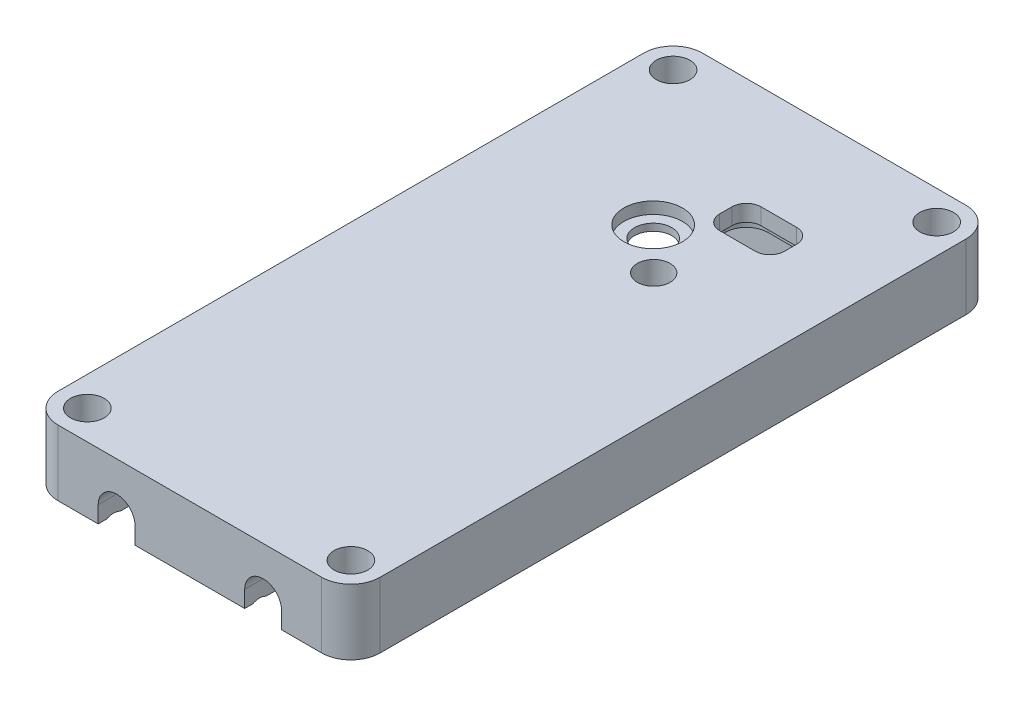
SolidWorks part; units mm, degrees
material "6061-T6 (SS)"
ref_plane "Front Plane" through (0, 0, 0) normal (0, 0, 1) x (1, 0, 0)
ref_plane "Top Plane" through (0, 0, 0) normal (0, 1, 0) x (1, 0, 0)
ref_plane "Right Plane" through (0, 0, 0) normal (1, 0, 0) x (0, 0, -1)
sketch "Sketch1" plane through (0, 0, 0) normal (0, 1, 0) x (1, 0, 0)
  line L1 (-14.127, 26.127) -> (14.127, 26.127) construction
  line L2 (-14.127, 26.127) -> (-14.127, -26.127) construction
  line L3 (-14.127, -26.127) -> (14.127, -26.127) construction
  line L4 (14.127, 26.127) -> (14.127, -26.127) construction
  line L5 (-14.127, 26.127) -> (14.127, -26.127) construction
  line L6 (-14.127, -26.127) -> (14.127, 26.127) construction
  line L7 (-17.4625, 34.925) -> (17.4625, 34.925)
  line L8 (-17.4625, 34.925) -> (-17.4625, -34.925)
  line L9 (-17.4625, -34.925) -> (17.4625, -34.925)
  line L10 (17.4625, 34.925) -> (17.4625, -34.925)
  line L11 (-17.4625, 34.925) -> (17.4625, -34.925) construction
  line L12 (-17.4625, -34.925) -> (17.4625, 34.925) construction
  point P0 (0, 0)
  point P6 (0, 0)
  dimension "D1" = 28.254
  dimension "D2" = 52.254
  dimension "D3" = 69.85
  dimension "D4" = 34.925
extrude "Boss-Extrude1" add sketch "Sketch1" along normal blind 7.112
fillet "Fillet1" radius 3.175 4 edges at (-17.4625, 3.556, -34.925) (17.4625, 3.556, -34.925) (17.4625, 3.556, 34.925) (-17.4625, 3.556, 34.925)
sketch "Sketch8" plane through (0, 0, 0) normal (0, 1, 0) x (1, 0, 0)
  line L0 (14.2875, 34.925) -> (-14.2875, 34.925) construction
  line L1 (-17.4625, 31.75) -> (-17.4625, -31.75) construction
  circle A0 centre (-1.2573, 21.6662) radius 2.3813
  dimension "D3" = 4.7625
  dimension "D1" = 13.2588
  dimension "D2" = 16.2052
extrude "Boss-Extrude2" add sketch "Sketch8" along normal up to surface (7.112 mm away) contours A0 up to face at (0, 7.112, 0)
sketch "Sketch9" plane through (0, 7.112, 0) normal (0, 1, 0) x (1, 0, 0)
  line L2 (-17.4625, 31.75) -> (-17.4625, -31.75) construction
  line L3 (14.2875, 34.925) -> (-14.2875, 34.925) construction
  circle A0 centre (-0.8255, 16.129) radius 2.0193
  dimension "D1" = 4.0386
  dimension "D2" = 18.796
  dimension "D3" = 16.637
extrude "Cut-Extrude6" cut sketch "Sketch9" against normal through all
sketch "Sketch12" plane through (0, 0, 0) normal (0, -1, 0) x (1, 0, 0)
  line L1 (14.127, 26.127) -> (-14.127, 26.127)
  line L2 (14.127, 26.127) -> (14.127, -26.127)
  line L3 (14.127, -26.127) -> (-14.127, -26.127)
  line L4 (-17.4625, 31.75) -> (-17.4625, -31.75)
  line L5 (-14.2875, -34.925) -> (14.2875, -34.925)
  line L6 (17.4625, -31.75) -> (17.4625, 31.75)
  line L7 (14.2875, 34.925) -> (-14.2875, 34.925)
  line L8 (-17.4625, 31.75) -> (-17.4625, -31.75)
  line L9 (-14.2875, -34.925) -> (14.2875, -34.925)
  line L10 (17.4625, -31.75) -> (17.4625, 31.75)
  line L11 (14.2875, 34.925) -> (-14.2875, 34.925)
  line L12 (-14.127, 26.127) -> (-14.127, -26.127)
  line L13 (14.127, 26.127) -> (-14.127, -26.127) construction
  line L14 (14.127, -26.127) -> (-14.127, 26.127) construction
  arc A4 (-17.4625, -31.75) -> (-14.2875, -34.925) centre (-14.2875, -31.75) ccw
  arc A5 (14.2875, -34.925) -> (17.4625, -31.75) centre (14.2875, -31.75) ccw
  arc A6 (17.4625, 31.75) -> (14.2875, 34.925) centre (14.2875, 31.75) ccw
  arc A7 (-14.2875, 34.925) -> (-17.4625, 31.75) centre (-14.2875, 31.75) ccw
  arc A8 (-17.4625, -31.75) -> (-14.2875, -34.925) centre (-14.2875, -31.75) ccw
  arc A9 (14.2875, -34.925) -> (17.4625, -31.75) centre (14.2875, -31.75) ccw
  arc A10 (17.4625, 31.75) -> (14.2875, 34.925) centre (14.2875, 31.75) ccw
  arc A11 (-14.2875, 34.925) -> (-17.4625, 31.75) centre (-14.2875, 31.75) ccw
  point P2 (0, 0)
  dimension "D2" = 52.254
  dimension "D3" = 28.254
  dimension "D1" = 0
extrude "Cut-Extrude8" cut sketch "Sketch12" against normal blind 4.318
fillet "Fillet2" radius 1.5875 4 edges at (-14.127, 2.159, 26.127) (-14.127, 2.159, -26.127) (14.127, 2.159, -26.127) (14.127, 2.159, 26.127)
sketch "Sketch16" plane through (0, 4.318, 0) normal (0, -1, 0) x (1, 0, 0)
  line L1 (7.789, 18.948) -> (-9.483, 18.948)
  line L2 (7.789, 18.948) -> (7.789, 2.946)
  line L3 (7.789, 2.946) -> (-9.483, 2.946)
  line L4 (-9.483, 18.948) -> (-9.483, 2.946)
  line L5 (7.789, 18.948) -> (-9.483, 2.946) construction
  line L6 (7.789, 2.946) -> (-9.483, 18.948) construction
  point P0 (-0.847, 10.947)
  dimension "D3" = 18.948
  dimension "D1" = 16.002
  dimension "D2" = 17.272
  dimension "D4" = 9.483
extrude "Boss-Extrude3" add sketch "Sketch16" along normal offset from surface (2.0574 mm away) 2.2606 up to face at (0, 0, 0)
sketch "Sketch25" plane through (0, 7.112, 0) normal (0, 1, 0) x (1, 0, 0)
  line L0 (-9.483, -15.3666) -> (7.789, -15.3666)
  line L1 (-9.483, -18.948) -> (7.789, -18.948)
  line L2 (-9.483, -18.948) -> (-9.483, -17.2716)
  line L3 (-9.483, -17.2716) -> (7.789, -17.2716)
  line L4 (7.789, -2.946) -> (-9.483, -2.946)
  line L5 (7.789, -18.948) -> (7.789, -2.946)
  line L6 (-9.483, -18.948) -> (7.789, -18.948)
  line L7 (-9.483, -2.946) -> (-9.483, -18.948)
  line L8 (7.789, -2.946) -> (-9.483, -2.946)
  line L9 (7.789, -18.948) -> (7.789, -2.946)
  line L10 (-9.483, -18.948) -> (7.789, -18.948)
  line L11 (-9.483, -2.946) -> (-9.483, -18.948)
  line L12 (7.789, -18.948) -> (7.789, -17.2716)
  line L13 (-9.483, -15.3666) -> (-9.483, -13.6902)
  line L14 (-9.483, -13.6902) -> (7.789, -13.6902)
  line L15 (7.789, -15.3666) -> (7.789, -13.6902)
  line L16 (-9.483, -11.7852) -> (7.789, -11.7852)
  line L17 (-9.483, -11.7852) -> (-9.483, -10.1088)
  line L18 (-9.483, -10.1088) -> (7.789, -10.1088)
  line L19 (7.789, -11.7852) -> (7.789, -10.1088)
  line L20 (-9.483, -8.2038) -> (7.789, -8.2038)
  line L21 (-9.483, -8.2038) -> (-9.483, -6.5274)
  line L22 (-9.483, -6.5274) -> (7.789, -6.5274)
  line L23 (7.789, -8.2038) -> (7.789, -6.5274)
  line L24 (-9.483, -4.6224) -> (7.789, -4.6224)
  line L25 (-9.483, -4.6224) -> (-9.483, -2.946)
  line L26 (-9.483, -2.946) -> (7.789, -2.946)
  line L27 (7.789, -4.6224) -> (7.789, -2.946)
  dimension "D2" = 1.905
  dimension "D1" = 0
  dimension "D3" = 5
extrude "Boss-Extrude4" [suppressed] add sketch "Sketch25" along normal offset from surface (4.0005 mm away) 11.1125 contours L1 L9 L3 L2 | L14 L11 L0 L9 | L18 L11 L16 L9 | L22 L11 L20 L9 | L11 L24 L9 L8
chamfer "Chamfer1" [suppressed] distance 4.7625 angle 45
sketch "Sketch31" plane through (0, 0, 0) normal (0, -1, 0) x (1, 0, 0)
  line L4 (-12.7, 28.575) -> (-13.0969, 28.575)
  line L5 (13.0969, 28.575) -> (12.7, 28.575)
  line L6 (16.2719, 25.4) -> (16.2719, -25.4)
  line L7 (13.0969, -28.575) -> (12.7, -28.575)
  line L8 (-16.2719, 25.4) -> (-16.2719, -25.4)
  line L9 (16.2719, 28.575) -> (-16.2719, -28.575) construction
  line L10 (16.2719, -28.575) -> (-16.2719, 28.575) construction
  line L11 (-9.525, 33.3375) -> (9.525, 33.3375)
  line L16 (-11.1125, 31.75) -> (-11.1125, 30.1625)
  line L18 (11.1125, 31.75) -> (11.1125, 30.1625)
  line L19 (-11.1125, 33.3375) -> (11.1125, 28.575) construction
  line L20 (-11.1125, 28.575) -> (11.1125, 33.3375) construction
  line L21 (-9.525, -33.3375) -> (9.525, -33.3375)
  line L22 (-11.1125, -31.75) -> (-11.1125, -30.1625)
  line L24 (11.1125, -31.75) -> (11.1125, -30.1625)
  line L25 (-11.1125, -33.3375) -> (11.1125, -28.575) construction
  line L26 (-11.1125, -28.575) -> (11.1125, -33.3375) construction
  line L27 (-12.7, -28.575) -> (-13.0969, -28.575)
  arc A4 (16.2719, -25.4) -> (13.0969, -28.575) centre (13.0969, -25.4) cw
  arc A5 (-13.0969, -28.575) -> (-16.2719, -25.4) centre (-13.0969, -25.4) cw
  arc A6 (-16.2719, 25.4) -> (-13.0969, 28.575) centre (-13.0969, 25.4) cw
  arc A7 (16.2719, 25.4) -> (13.0969, 28.575) centre (13.0969, 25.4) ccw
  arc A8 (12.7, -28.575) -> (11.1125, -30.1625) centre (12.7, -30.1625) ccw
  arc A9 (11.1125, -31.75) -> (9.525, -33.3375) centre (9.525, -31.75) cw
  arc A10 (-11.1125, -31.75) -> (-9.525, -33.3375) centre (-9.525, -31.75) ccw
  arc A11 (-12.7, -28.575) -> (-11.1125, -30.1625) centre (-12.7, -30.1625) cw
  arc A16 (-11.1125, 31.75) -> (-9.525, 33.3375) centre (-9.525, 31.75) cw
  arc A17 (-11.1125, 30.1625) -> (-12.7, 28.575) centre (-12.7, 30.1625) cw
  arc A18 (12.7, 28.575) -> (11.1125, 30.1625) centre (12.7, 30.1625) cw
  arc A19 (11.1125, 31.75) -> (9.525, 33.3375) centre (9.525, 31.75) ccw
  point P0 (0, 0)
  point P17 (0, 30.9563)
  point P22 (0, -30.9563)
  dimension "D3" = 3.175
  dimension "D4" = 1.5875
  dimension "D1" = 32.5437
  dimension "D2" = 57.15
  dimension "D5" = 66.675
  dimension "D6" = 22.225
sketch "Sketch32" plane through (0, 0, 0) normal (1, 0, 0) x (0, 0, -1)
  line L0 (34.925, 0) -> (26.127, 0)
  line L1 (-26.127, 0) -> (-34.925, 0)
  line L2 (-26.127, 0) -> (-34.925, 0)
  line L4 (34.925, 0) -> (26.127, 0)
  circle A0 centre (-33.3375, -1.4097) radius 1.5875
  point P0 (-33.3375, 0)
  point P6 (-33.3375, 0.1778)
  dimension "D1" = 3.175
  dimension "D3" = 0.1778
sweep "Cut-Sweep1" cut profiles "Sketch32" path "Sketch31"
sketch "Sketch15" plane through (0, 0, -34.925) normal (0, 0, -1) x (-1, 0, 0)
  line L0 (-7.9463, 0) -> (-7.9463, 1.8) construction
  line L1 (-14.2875, 0) -> (14.2875, 0) construction
  line L2 (-9.9463, 0) -> (-9.9463, 1.8)
  line L3 (-5.9463, 0) -> (-5.9463, 1.8)
  line L4 (7.9375, 0) -> (7.9375, 1.8) construction
  line L5 (5.9375, 0) -> (5.9375, 1.8)
  line L6 (9.9375, 0) -> (9.9375, 1.8)
  line L9 (-14.2875, 7.112) -> (-14.2875, 0) construction
  line L10 (14.2875, 0) -> (14.2875, 7.112) construction
  arc A0 (-9.9463, 0) -> (-5.9463, 0) centre (-7.9463, 0) ccw
  arc A1 (-5.9463, 1.8) -> (-9.9463, 1.8) centre (-7.9463, 1.8) ccw
  arc A2 (5.9375, 0) -> (9.9375, 0) centre (7.9375, 0) ccw
  arc A3 (9.9375, 1.8) -> (5.9375, 1.8) centre (7.9375, 1.8) ccw
  point P4 (-7.9463, 0.9)
  point P9 (7.9375, 0.9)
  point P17 (-7.9463, 3.8)
  dimension "D1" = 4
  dimension "D2" = 3.8
  dimension "D3" = 6.3412
  dimension "D4" = 6.35
extrude "Cut-Extrude10" cut sketch "Sketch15" against normal through all contours L3 A1 L2 A0 | L6 A3 L5 A2
hole_wizard "#6 Clearance Hole1" positions "Sketch33" profile "Sketch35" hole size "#6" standard "ANSI Inch" end condition through all
sketch "Sketch33" plane through (0, 7.112, 0) normal (0, 1, 0) x (1, 0, 0)
  point P0 (-14.2875, -31.75)
  point P3 (-14.2875, 31.75)
  point P6 (14.2875, 31.75)
  point P9 (14.2875, -31.75)
sketch "Sketch35" plane through (-14.2875, 7.112, 31.75) normal (1, 0, 0) x (0, 0, 1)
  line L0 (0, 0) -> (0, 7.112)
  line L1 (0, 7.112) -> (1.8288, 7.112)
  line L2 (1.8288, 7.112) -> (1.8288, 0)
  line L5 (1.8288, 0) -> (0, 0)
  line L11 (0, -6.35) -> (0, 107.95) construction
  dimension "Thru Hole Dia." = 3.6576
  dimension "Thru Hole Depth" = 7.112
sketch "Sketch36" plane through (0, 0, 0) normal (0, -1, 0) x (1, 0, 0)
  line L0 (5.9463, 26.127) -> (-5.9375, 26.127) construction
  line L1 (-4.0413, 30.1625) -> (4.0413, 30.1625)
  line L2 (-4.0413, 30.1625) -> (-4.0413, 26.127)
  line L3 (-4.0413, 26.127) -> (4.0413, 26.127)
  line L4 (4.0413, 30.1625) -> (4.0413, 26.127)
  line L5 (-4.0413, 30.1625) -> (4.0413, 26.127) construction
  line L6 (-4.0413, 26.127) -> (4.0413, 30.1625) construction
  line L7 (5.9463, 32.6075) -> (5.9463, 26.127) construction
  line L8 (-5.9375, 34.925) -> (5.9463, 34.925) construction
  point P0 (0, 28.1447)
  dimension "D1" = 1.905
  dimension "D2" = 4.7625
extrude "Cut-Extrude17" cut sketch "Sketch36" against normal up to surface (4.318 mm away) up to face at (-0.8255, 4.318, -18.1483)
fillet "Fillet3" radius 1.5875 4 edges at (-4.0413, 2.159, 30.1625) (-4.0413, 2.159, 26.127) (4.0413, 2.159, 30.1625) (4.0413, 2.159, 26.127)
sketch "Sketch37" plane through (0, 4.318, 0) normal (0, -1, 0) x (1, 0, 0)
  line L0 (8.3104, -21.428) -> (8.7754, -21.428) construction
  line L1 (2.2144, -19.65) -> (8.3104, -19.65) construction
  line L2 (2.2144, -19.65) -> (2.2144, -23.206) construction
  line L3 (2.2144, -23.206) -> (8.3104, -23.206) construction
  line L4 (8.3104, -19.65) -> (8.3104, -23.206) construction
  line L5 (2.2144, -19.65) -> (8.3104, -23.206) construction
  line L6 (2.2144, -23.206) -> (8.3104, -19.65) construction
  line L7 (7.1879, -23.671) -> (3.3369, -23.671)
  line L8 (14.127, 24.5395) -> (14.127, -24.5395) construction
  line L9 (12.5395, -26.127) -> (-12.5395, -26.127) construction
  line L10 (8.7754, -22.0835) -> (8.7754, -20.7725)
  line L11 (7.1879, -19.185) -> (3.3369, -19.185)
  line L12 (1.7494, -22.0835) -> (1.7494, -20.7725)
  line L14 (5.2624, -23.671) -> (5.2624, -23.206) construction
  arc A0 (3.3369, -23.671) -> (1.7494, -22.0835) centre (3.3369, -22.0835) cw
  arc A1 (1.7494, -20.7725) -> (3.3369, -19.185) centre (3.3369, -20.7725) cw
  arc A2 (7.1879, -19.185) -> (8.7754, -20.7725) centre (7.1879, -20.7725) cw
  arc A3 (8.7754, -22.0835) -> (7.1879, -23.671) centre (7.1879, -22.0835) cw
  point P0 (5.2624, -21.428)
  point P5 (5.2624, -21.428)
  dimension "D5" = 1.5875
  dimension "D1" = 5.8166
  dimension "D2" = 6.096
  dimension "D3" = 2.921
  dimension "D4" = 6.477
extrude "Cut-Extrude18" cut sketch "Sketch37" against normal through all
sketch "Sketch38" plane through (0, 4.318, 0) normal (0, -1, 0) x (1, 0, 0)
  line L1 (-10.317, 0.797) -> (-7.142, 0.797) construction
  line L2 (-10.317, 0.797) -> (-10.317, -3.648) construction
  line L3 (-10.317, -3.648) -> (-7.142, -3.648) construction
  line L4 (-7.142, 0.797) -> (-7.142, -3.648) construction
  line L5 (-10.317, 0.797) -> (-7.142, -3.648) construction
  line L6 (-10.317, -3.648) -> (-7.142, 0.797) construction
  line L8 (12.5395, -26.127) -> (-12.5395, -26.127) construction
  line L10 (-14.127, 24.5395) -> (-14.127, -24.5395) construction
  circle A0 centre (-8.7295, -1.4255) radius 3.175
  point P0 (-8.7295, -1.4255)
  dimension "D5" = 6.35
  dimension "D1" = 3.175
  dimension "D2" = 6.985
  dimension "D3" = 26.924
  dimension "D4" = 22.479
extrude "Cut-Extrude19" cut sketch "Sketch38" against normal offset from surface (1.2446 mm away) 3.302 up to face at (0.0044, 2.2606, 10.947)
sketch "Sketch39" plane through (0, 4.318, 0) normal (0, -1, 0) x (1, 0, 0)
  line L1 (14.127, 24.5395) -> (14.127, -24.5395) construction
  line L2 (12.5395, -26.127) -> (-12.5395, -26.127) construction
  circle A0 centre (3.713, -11.649) radius 1.778
  dimension "D1" = 3.556
  dimension "D2" = 14.478
  dimension "D3" = 10.414
extrude "Cut-Extrude20" cut sketch "Sketch39" against normal offset from surface (2.8956 mm away) 1.651 up to face at (-8.7295, 5.5626, 1.7495)
sketch "Sketch40" plane through (0, 4.318, 0) normal (0, -1, 0) x (1, 0, 0)
  line L1 (12.5395, 26.127) -> (9.9463, 26.127) construction
  line L2 (14.127, 26.127) -> (13.0045, 25.0045) construction
  line L3 (0, 30.1625) -> (0, -26.127) construction
  line L4 (-2.4538, 30.1625) -> (2.4538, 30.1625) construction
  line L6 (0, 0) -> (14.127, 0) construction
  line L7 (12.5395, -26.127) -> (-12.5395, -26.127) construction
  line L8 (14.127, 24.5395) -> (14.127, -24.5395) construction
  line L9 (14.127, 24.5395) -> (14.127, -24.5395) construction
  circle A0 centre (13.0045, 25.0045) radius 1.5875
  arc A1 (14.127, 24.5395) -> (12.5395, 26.127) centre (12.5395, 24.5395) ccw construction
  circle A2 centre (13.0045, -25.0045) radius 1.5875
  circle A3 centre (-13.0045, -25.0045) radius 1.5875
  circle A4 centre (-13.0045, 25.0045) radius 1.5875
  point P0 (14.127, 26.127)
  point P11 (13.662, 25.662)
  dimension "D1" = 3.175
extrude "Cut-Extrude21" cut sketch "Sketch40" along normal through all
sketch "Sketch41" plane through (0, 7.112, 0) normal (0, 1, 0) x (1, 0, 0)
  circle A0 centre (-0.8255, 16.129) radius 3.175
  dimension "D1" = 6.35
extrude "Cut-Extrude22" cut sketch "Sketch41" against normal blind 1.27
sketch "Sketch42" plane through (0, 4.318, 0) normal (0, -1, 0) x (1, 0, 0)
  circle A0 centre (-0.8255, -16.129) radius 3.175
  circle A1 centre (-0.8255, -16.129) radius 3.175 construction
extrude "Cut-Extrude23" cut sketch "Sketch42" against normal blind 0.762
sketch "Sketch43" plane through (0, 4.318, 0) normal (0, -1, 0) x (1, 0, 0)
  line L8 (0.9874, -20.7725) -> (0.9874, -22.0835)
  line L9 (7.1879, -18.423) -> (3.3369, -18.423)
  line L10 (9.5374, -22.0835) -> (9.5374, -20.7725)
  line L11 (3.3369, -24.433) -> (7.1879, -24.433)
  line L12 (0.9874, -20.7725) -> (0.9874, -22.0835)
  line L13 (7.1879, -18.423) -> (3.3369, -18.423)
  line L14 (9.5374, -22.0835) -> (9.5374, -20.7725)
  line L15 (3.3369, -24.433) -> (7.1879, -24.433)
  arc A8 (3.3369, -18.423) -> (0.9874, -20.7725) centre (3.3369, -20.7725) ccw
  arc A9 (9.5374, -20.7725) -> (7.1879, -18.423) centre (7.1879, -20.7725) ccw
  arc A10 (7.1879, -24.433) -> (9.5374, -22.0835) centre (7.1879, -22.0835) ccw
  arc A11 (0.9874, -22.0835) -> (3.3369, -24.433) centre (3.3369, -22.0835) ccw
  arc A12 (3.3369, -18.423) -> (0.9874, -20.7725) centre (3.3369, -20.7725) ccw
  arc A13 (9.5374, -20.7725) -> (7.1879, -18.423) centre (7.1879, -20.7725) ccw
  arc A14 (7.1879, -24.433) -> (9.5374, -22.0835) centre (7.1879, -22.0835) ccw
  arc A15 (0.9874, -22.0835) -> (3.3369, -24.433) centre (3.3369, -22.0835) ccw
  dimension "D1" = 0.762
extrude "Cut-Extrude24" cut sketch "Sketch43" against normal blind 1.016
equation "\"D1@Sketch1\"=28mm+.01"
equation "\"D2@Sketch1\"=52mm+.01"
equation "\"D1@Sketch8\"=.125+.397"
equation "\"D2@Sketch8\"=.125+.513"
equation "\"D2@Sketch12\"=52mm+.01"
equation "\"D3@Sketch12\"=28mm+.01"
